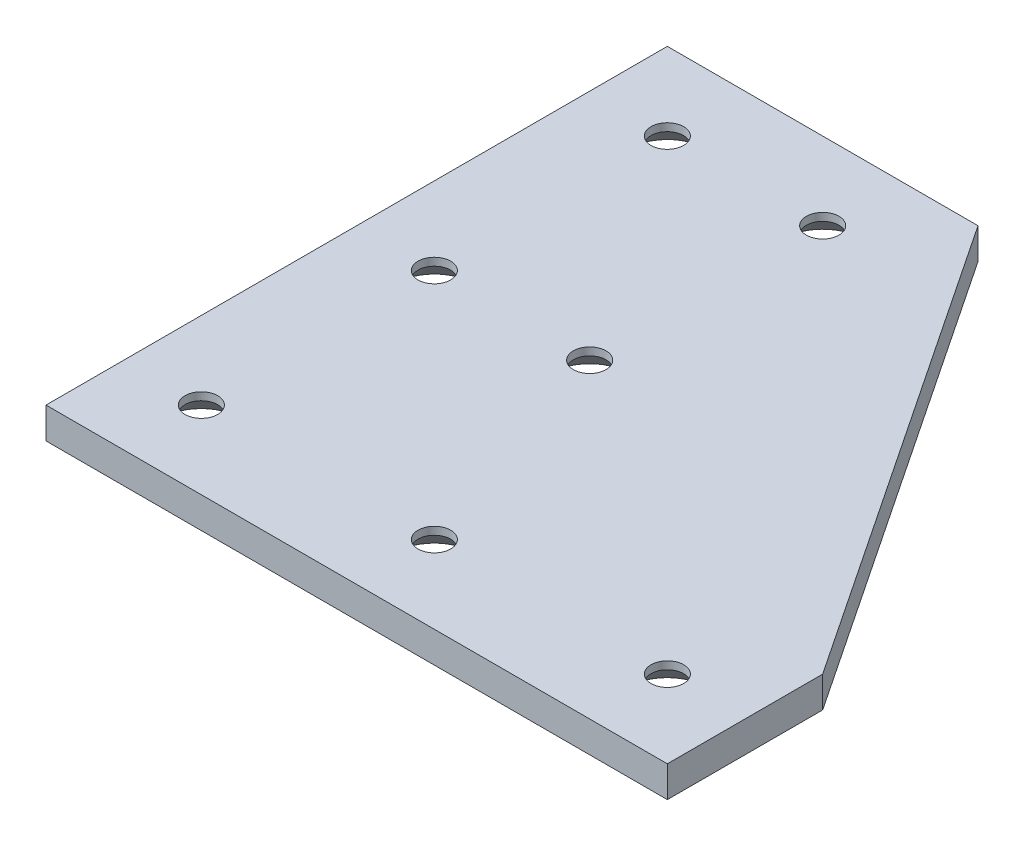
SolidWorks part; units mm, degrees
material "1060 Alloy"
ref_plane "Front Plane" through (0, 0, 0) normal (0, 0, 1) x (1, 0, 0)
ref_plane "Top Plane" through (0, 0, 0) normal (0, 1, 0) x (1, 0, 0)
ref_plane "Right Plane" through (0, 0, 0) normal (1, 0, 0) x (0, 0, -1)
sketch "Sketch1" plane through (0, 0, 0) normal (0, 1, 0) x (1, 0, 0)
  line L0 (0, 0) -> (80, 0)
  line L1 (80, 0) -> (80, 20)
  line L2 (80, 20) -> (40, 80)
  line L3 (40, 80) -> (0, 80)
  line L4 (0, 80) -> (0, 0)
  point P0 (40, 79.8999)
  point P8 (0, 80)
  point P11 (40, 80)
  point P14 (80, 20)
  point P17 (80, 0)
  point P20 (0, 0)
  dimension "D1" = 80
  dimension "D2" = 80
  dimension "D3" = 20
  dimension "D4" = 40
extrude "Boss-Extrude1" add sketch "Sketch1" along normal blind 4
sketch "Sketch2" plane through (0, 4, 0) normal (0, 1, 0) x (1, 0, 0)
  line L0 (0, 0) -> (80, 0) construction
  line L1 (0, 80) -> (0, 0) construction
  line L2 (80, 0) -> (80, 20) construction
  line L3 (40, 80) -> (0, 80) construction
  circle A0 centre (10, 10) radius 2.1
  circle A1 centre (40, 10) radius 2.1
  circle A2 centre (70, 10) radius 2.1
  circle A4 centre (30, 40) radius 2.1
  circle A5 centre (30, 70) radius 2.1
  circle A6 centre (10, 40) radius 2.1
  circle A7 centre (10, 70) radius 2.1
  circle A8 centre (30, 10) radius 2.1 [skipped]
  dimension "D1" = 4.2
  dimension "D3" = 3
  dimension "D2" = 10
  dimension "10" = 10
  dimension "D4" = 10
  dimension "D7" = 10
  dimension "D8" = 10
  dimension "D9" = 20
  dimension "D5" = 2
  dimension "D6" = 3
extrude "Cut-Extrude1" cut sketch "Sketch2" against normal blind 4
chamfer "Chamfer1" distance 3 angle 45 7 edges at (10, 0, -67.9) (30, 0, -67.9) (30, 0, -37.9) (10, 0, -37.9) (10, 0, -7.9) (40, 0, -7.9) (70, 0, -7.9)
fillet "Fillet1" [suppressed] radius 1
